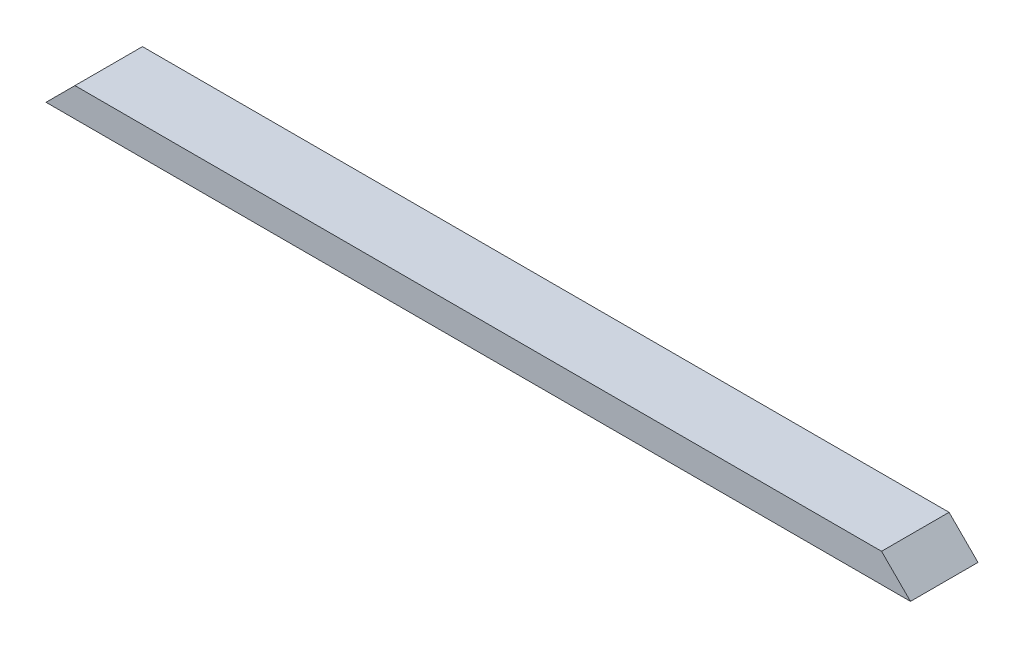
SolidWorks part; units mm, degrees
material "Pine"
ref_plane "Front Plane" through (0, 0, 0) normal (0, 0, 1) x (1, 0, 0)
ref_plane "Top Plane" through (0, 0, 0) normal (0, 1, 0) x (1, 0, 0)
ref_plane "Right Plane" through (0, 0, 0) normal (1, 0, 0) x (0, 0, -1)
sketch "Sketch1" plane through (0, 0, 0) normal (0, 1, 0) x (1, 0, 0)
  line L1 (0, 0) -> (1138.2375, 0)
  line L2 (0, 0) -> (0, 88.9)
  line L3 (0, 88.9) -> (1138.2375, 88.9)
  line L4 (1138.2375, 0) -> (1138.2375, 88.9)
  dimension "D1" = 88.9
  dimension "D2" = 1138.2375
extrude "Boss-Extrude1" add sketch "Sketch1" along normal blind 38.1
sketch "Sketch2" plane through (0, 0, 0) normal (0, 0, 1) x (1, 0, 0)
  line L0 (0, 0) -> (38.1, 38.1)
  line L1 (0, 38.1) -> (1138.2375, 38.1) construction
  line L2 (38.1, 38.1) -> (0, 38.1)
  line L3 (0, 38.1) -> (0, 0)
  line L5 (1138.2375, 0) -> (1138.2375, 38.1)
  line L9 (1138.2375, 38.1) -> (1100.1375, 38.1)
  line L10 (1100.1375, 38.1) -> (1138.2375, 0)
  dimension "D1" = 38.1
  dimension "D2" = 38.1
  dimension "D3" = 38.1
extrude "Cut-Extrude1" cut sketch "Sketch2" against normal through all
